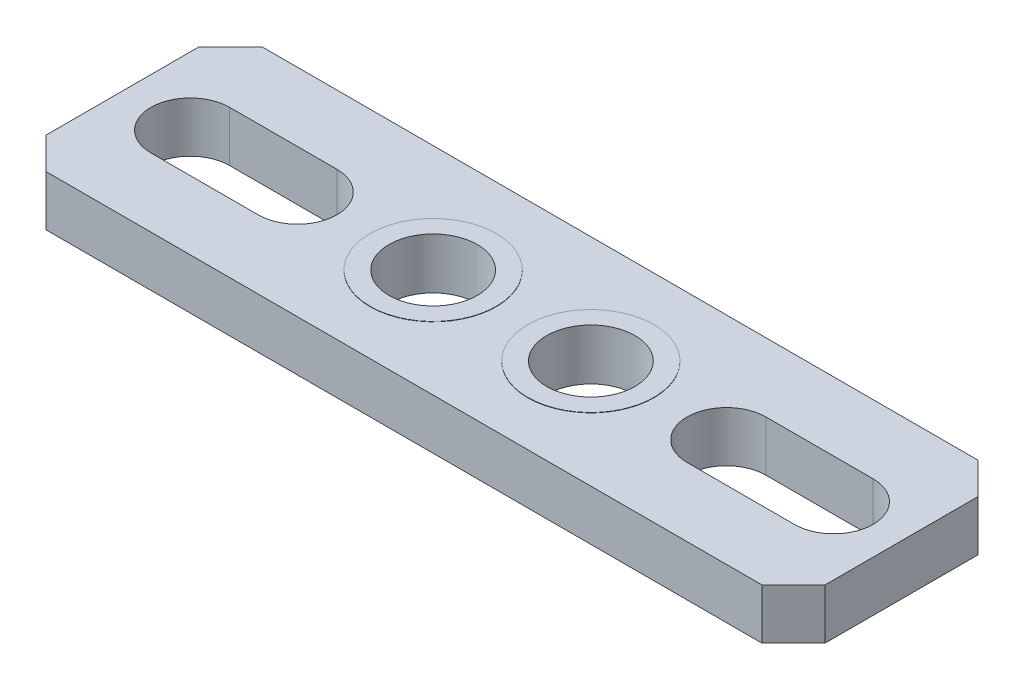
SolidWorks part; units mm, degrees
ref_plane "Front Plane" through (0, 0, 0) normal (0, 0, 1) x (1, 0, 0)
ref_plane "Top Plane" through (0, 0, 0) normal (0, 1, 0) x (1, 0, 0)
ref_plane "Right Plane" through (0, 0, 0) normal (1, 0, 0) x (0, 0, -1)
sketch "Sketch1" plane through (0, 0, 0) normal (0, 1, 0) x (1, 0, 0)
  line L0 (-12.35, 0) -> (12.35, 0) construction
  line L1 (-12.35, 3.425) -> (12.35, 3.425)
  line L2 (-12.35, 3.425) -> (-12.35, -3.425)
  line L3 (-12.35, -3.425) -> (12.35, -3.425)
  line L4 (12.35, 3.425) -> (12.35, -3.425)
  line L5 (-12.35, 3.425) -> (12.35, -3.425) construction
  line L6 (-12.35, -3.425) -> (12.35, 3.425) construction
  line L7 (0, 3.425) -> (0, -3.425) construction
  line L8 (-10.2, 0) -> (-6.8, 0) construction
  line L9 (-10.2, 1.25) -> (-6.8, 1.25)
  line L10 (-10.2, -1.25) -> (-6.8, -1.25)
  line L11 (10.2, 0) -> (6.8, 0) construction
  line L12 (10.2, 1.25) -> (6.8, 1.25)
  line L13 (10.2, -1.25) -> (6.8, -1.25)
  circle A0 centre (-2.5, 0) radius 1.4
  circle A1 centre (2.5, 0) radius 1.4
  arc A2 (-10.2, 1.25) -> (-10.2, -1.25) centre (-10.2, 0) ccw
  arc A3 (-6.8, -1.25) -> (-6.8, 1.25) centre (-6.8, 0) ccw
  arc A4 (10.2, 1.25) -> (10.2, -1.25) centre (10.2, 0) cw
  arc A5 (6.8, -1.25) -> (6.8, 1.25) centre (6.8, 0) cw
  point P0 (0, 0)
  point P16 (-8.5, 0)
  point P21 (-11.45, 0)
  point P22 (-5.55, 0)
  point P25 (8.5, 0)
  dimension "D4" = 2.8
  dimension "D1" = 24.7
  dimension "D2" = 6.85
  dimension "D3" = 5
  dimension "D5" = 2.5
  dimension "D6" = 17
  dimension "D7" = 5.9
extrude "Boss-Extrude1" add sketch "Sketch1" along normal mid plane 1.6
chamfer "Chamfer1" distance 1 angle 45 4 edges at (-12.35, 0, -3.425) (12.35, 0, -3.425) (12.35, 0, 3.425) (-12.35, 0, 3.425)
sketch "Sketch2" plane through (0, 0.8, 0) normal (0, 1, 0) x (1, 0, 0)
  circle A0 centre (-2.5, 0) radius 2
  circle A1 centre (2.5, 0) radius 2
  circle A2 centre (2.5, 0) radius 1.4 construction
  circle A3 centre (-2.5, 0) radius 1.4 construction
  circle A4 centre (2.5, 0) radius 1.4
  circle A5 centre (-2.5, 0) radius 1.4
  dimension "D1" = 4
extrude "Boss-Extrude2" add sketch "Sketch2" along normal blind 0.01
mirror "Mirror1" about plane through (0, 0, 0) normal (0, 1, 0) of "Boss-Extrude2"
